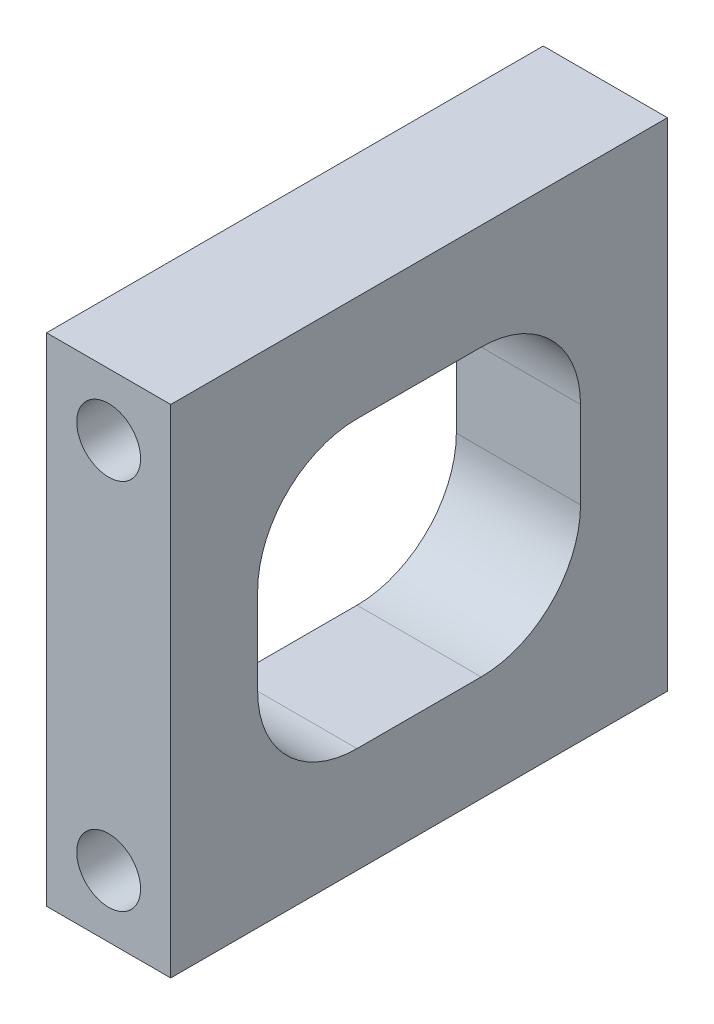
SolidWorks part; units mm, degrees
ref_plane "Front Plane" through (0, 0, 0) normal (0, 0, 1) x (1, 0, 0)
ref_plane "Top Plane" through (0, 0, 0) normal (0, 1, 0) x (1, 0, 0)
ref_plane "Right Plane" through (0, 0, 0) normal (1, 0, 0) x (0, 0, -1)
sketch "Sketch1" plane through (0, 0, 0) normal (0, 0, 1) x (1, 0, 0)
  line L1 (0, 0) -> (12.7, 0)
  line L2 (0, 0) -> (0, 50.8)
  line L3 (0, 50.8) -> (12.7, 50.8)
  line L4 (12.7, 0) -> (12.7, 50.8)
  dimension "D1" = 12.7
  dimension "D2" = 50.8
extrude "Boss-Extrude1" add sketch "Sketch1" along normal blind 50.8
sketch "Sketch2" plane through (0, 0, 50.8) normal (0, 0, 1) x (1, 0, 0)
  line L0 (0, 0) -> (12.7, 0) construction
  line L1 (12.7, 0) -> (12.7, 50.8) construction
  circle A0 centre (6.35, 44.45) radius 3.2639
  circle A1 centre (6.35, 6.35) radius 3.2639
  point P4 (6.35, 0)
  point P5 (6.35, 44.7827)
  point P9 (12.7, 25.4)
  dimension "D1" = 6.5278
  dimension "D2" = 38.1
  dimension "D3" = 19.05
extrude "Cut-Extrude1" cut sketch "Sketch2" against normal blind 19.05 contours A0 | A1
ref_plane "Plane1" through (0, 0, 25.4) normal (0, 0, 1) x (1, 0, 0)
mirror "Mirror1" about plane through (0, 0, 25.4) normal (0, 0, 1) of "Cut-Extrude1"
sketch "Sketch3" plane through (0, 0, 0) normal (-1, 0, 0) x (0, 0, 1)
  line L1 (8.89, 40.005) -> (41.91, 40.005)
  line L2 (8.89, 40.005) -> (8.89, 10.795)
  line L3 (8.89, 10.795) -> (41.91, 10.795)
  line L4 (41.91, 40.005) -> (41.91, 10.795)
  line L5 (0, 50.8) -> (0, 0) construction
  line L6 (50.8, 50.8) -> (0, 50.8) construction
  point P4 (0, 25.4)
  point P5 (8.89, 25.4)
  point P8 (25.4, 50.8)
  point P9 (25.4, 40.005)
  point P12 (0, 0)
  point P13 (0, 0)
  dimension "D1" = 29.21
  dimension "D2" = 33.02
extrude "Cut-Extrude2" cut sketch "Sketch3" against normal through all
fillet "Fillet1" radius 10.16 4 edges at (6.35, 10.795, 41.91) (6.35, 10.795, 8.89) (6.35, 40.005, 41.91) (6.35, 40.005, 8.89)
